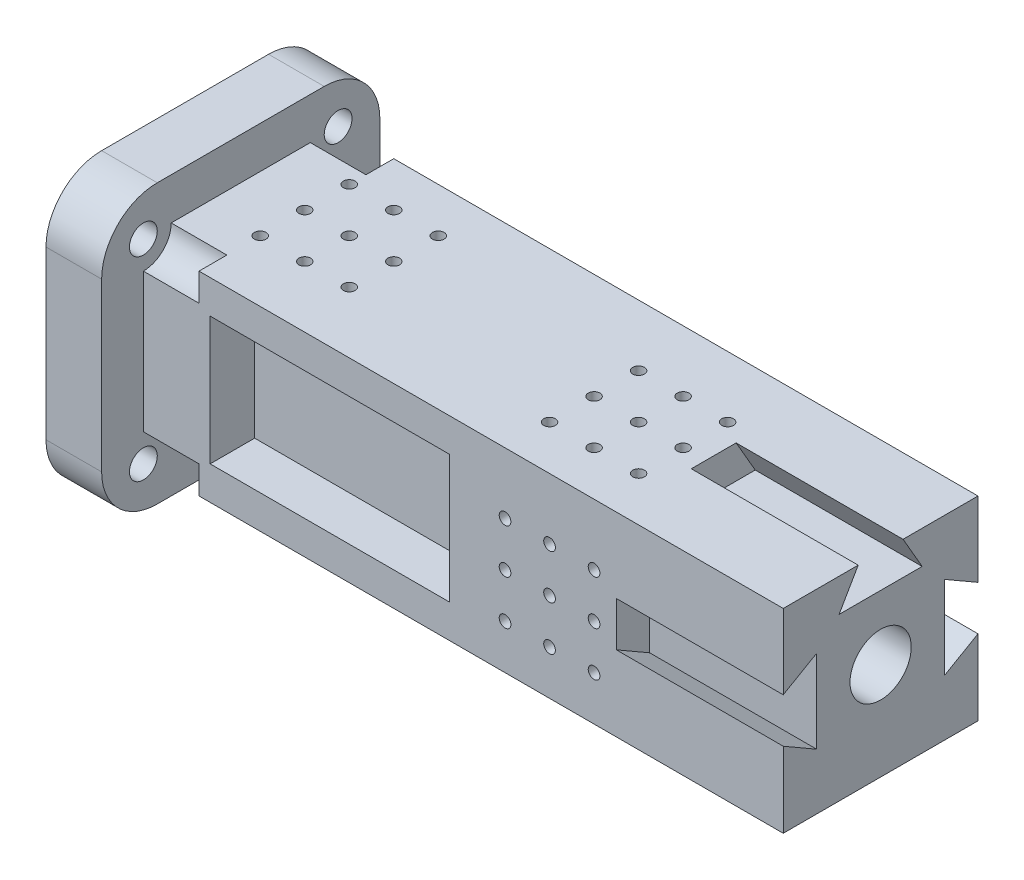
SolidWorks part; units mm, degrees
ref_plane "Front Plane" through (0, 0, 0) normal (0, 0, 1) x (1, 0, 0)
ref_plane "Top Plane" through (0, 0, 0) normal (0, 1, 0) x (1, 0, 0)
ref_plane "Right Plane" through (0, 0, 0) normal (1, 0, 0) x (0, 0, -1)
sketch "Sketch1" plane through (0, 0, 0) normal (1, 0, 0) x (0, 0, -1)
  line L1 (0, 0) -> (35, 0)
  line L2 (0, 0) -> (0, 35)
  line L3 (0, 35) -> (35, 35)
  line L4 (35, 0) -> (35, 35)
  circle A0 centre (17.5, 17.5) radius 5.5
  point P7 (35, 17.5)
  point P9 (17.5, 0)
  dimension "D3" = 11
  dimension "D1" = 35
  dimension "D2" = 35
extrude "Boss-Extrude1" add sketch "Sketch1" along normal blind 115
sketch "Sketch2" plane through (115, 0, 0) normal (1, 0, 0) x (0, 0, -1)
  line L0 (0, 13.5534) -> (6, 10.0893)
  line L1 (0, 35) -> (0, 0) construction
  line L2 (6, 10.0893) -> (6, 25.0175)
  line L3 (6, 25.0175) -> (0, 21.5534)
  line L5 (0.0267, 17.5534) -> (15.3791, 17.5534) construction
  line L6 (17.5, 0.0534) -> (17.5, 32.5624) construction
  line L7 (0, 0) -> (35, 0) construction
  line L20 (0, 21.5534) -> (-1, 21.5534)
  line L21 (-1, 21.5534) -> (-1, 13.5534)
  line L22 (-1, 13.5534) -> (0, 13.5534)
  line L23 (21.5, 35.0534) -> (21.5, 36.0534)
  line L24 (21.5, 36.0534) -> (13.5, 36.0534)
  line L25 (13.5, 36.0534) -> (13.5, 35.0534)
  line L26 (13.5, 35.0534) -> (10.0359, 29.0534)
  line L27 (10.0359, 29.0534) -> (24.9641, 29.0534)
  line L28 (24.9641, 29.0534) -> (21.5, 35.0534)
  line L29 (35, 13.5534) -> (36, 13.5534)
  line L30 (36, 13.5534) -> (36, 21.5534)
  line L31 (36, 21.5534) -> (35, 21.5534)
  line L32 (35, 21.5534) -> (29, 25.0175)
  line L33 (29, 25.0175) -> (29, 10.0893)
  line L34 (29, 10.0893) -> (35, 13.5534)
  line L41 (24.9641, 6.0534) -> (10.0359, 6.0534) [skipped]
  line L42 (10.0359, 6.0534) -> (13.5, 0.0534) [skipped]
  line L43 (13.5, -0.9466) -> (21.5, -0.9466) [skipped]
  line L44 (13.5, 0.0534) -> (13.5, -0.9466) [skipped]
  line L45 (21.5, -0.9466) -> (21.5, 0.0534) [skipped]
  line L46 (21.5, 0.0534) -> (24.9641, 6.0534) [skipped]
  point P27 (17.5, 17.5534)
  point P36 (17.5, 17.5534)
  dimension "D1" = 60
  dimension "D2" = 60
  dimension "D3" = 8
  dimension "D4" = 1
  dimension "D5" = 4
  dimension "D6" = 17.5534
  dimension "D7" = 17.5
  dimension "D9" = 4
  dimension "D10" = 4
  dimension "D11" = 6
  dimension "D8" = 4
extrude "Cut-Extrude2" cut sketch "Sketch2" against normal blind 30
sketch "Sketch3" plane through (0, 0, 0) normal (-1, 0, 0) x (0, 0, 1)
  line L1 (-42.5, -7.5) -> (7.5, -7.5)
  line L2 (-42.5, -7.5) -> (-42.5, 42.5)
  line L3 (-42.5, 42.5) -> (7.5, 42.5)
  line L4 (7.5, -7.5) -> (7.5, 42.5)
  line L5 (-42.5, -7.5) -> (7.5, 42.5) construction
  line L6 (-42.5, 42.5) -> (7.5, -7.5) construction
  circle A0 centre (-17.5, 17.5) radius 5.5
  point P0 (-17.5, 17.5)
  dimension "D3" = 11
  dimension "D1" = 50
  dimension "D2" = 50
extrude "Boss-Extrude2" add sketch "Sketch3" along normal blind 10
sketch "Sketch4" plane through (-10, 0, 0) normal (-1, 0, 0) x (0, 0, 1)
  circle A1 centre (-35, 35) radius 2.5
  circle A2 centre (-35, 0) radius 2.5
  circle A3 centre (0, 0) radius 2.5
  circle A4 centre (0, 35) radius 2.5
  point P14 (-17.5, 17.5)
  dimension "D1" = 17.5
  dimension "D2" = 5
  dimension "D4" = 17.5
  dimension "D3" = 4
extrude "Cut-Extrude3" cut sketch "Sketch4" against normal blind 15
sketch "Sketch6" plane through (0, 0, 0) normal (0, 0, 1) x (-1, 0, 0)
  line L0 (0, -16) -> (-257.9227, -16) construction
  line L1 (-115, -13.5534) -> (-115, 0) construction
  line L3 (-115, -35) -> (-5, -35) construction
  circle A0 centre (-65, -8) radius 1.05
  circle A1 centre (-73, -8) radius 1.05
  circle A2 centre (-81, -8) radius 1.05
  circle A3 centre (-73, -16) radius 1.05
  circle A4 centre (-81, -16) radius 1.05
  circle A5 centre (-73, -24) radius 1.05
  circle A6 centre (-81, -24) radius 1.05
  circle A7 centre (-65, -16) radius 1.05
  circle A8 centre (-65, -24) radius 1.05
  dimension "D3" = 2.1
  dimension "D4" = 8
  dimension "D5" = 8
  dimension "D6" = 34
  dimension "D7" = 19
  dimension "D1" = 3
  dimension "D2" = 3
sketch "Sketch7" plane through (0, 35, 0) normal (0, 1, 0) x (-1, 0, 0)
  line L0 (0, -16) -> (-231.7822, -16) construction
  line L3 (-115, -35) -> (-5, -35) construction
  line L4 (-115, -13.4692) -> (-115, 0) construction
  circle A0 centre (-65, -8) radius 1.05
  circle A1 centre (-73, -8) radius 1.05
  circle A2 centre (-81, -8) radius 1.05
  circle A3 centre (-73, -16) radius 1.05
  circle A4 centre (-81, -16) radius 1.05
  circle A5 centre (-73, -24) radius 1.05
  circle A6 centre (-81, -24) radius 1.05
  circle A7 centre (-65, -16) radius 1.05
  circle A8 centre (-65, -24) radius 1.05
  dimension "D3" = 2.1
  dimension "D4" = 8
  dimension "D5" = 8
  dimension "D6" = 34
  dimension "D7" = 19
  dimension "D1" = 3
  dimension "D2" = 3
sketch "Sketch8" plane through (0, 0, -35) normal (0, 0, -1) x (1, 0, 0)
  line L0 (0, -19) -> (262.5218, -19) construction
  line L2 (115, 0) -> (5, 0) construction
  line L3 (115, 0) -> (115, -13.5534) construction
  circle A0 centre (81, -11) radius 1.05
  circle A1 centre (73, -11) radius 1.05
  circle A2 centre (65, -11) radius 1.05
  circle A3 centre (73, -19) radius 1.05
  circle A4 centre (65, -19) radius 1.05
  circle A5 centre (73, -27) radius 1.05
  circle A6 centre (65, -27) radius 1.05
  circle A7 centre (81, -19) radius 1.05
  circle A8 centre (81, -27) radius 1.05
  dimension "D3" = 2.1
  dimension "D4" = 8
  dimension "D5" = 8
  dimension "D6" = 34
  dimension "D7" = 19
  dimension "D1" = 3
  dimension "D2" = 3
sketch "Sketch9" plane through (0, 0, 0) normal (0, -1, 0) x (1, 0, 0)
  line L0 (0, -19) -> (216.7478, -19) construction
  line L1 (115, 0) -> (115, -35) construction
  line L2 (115, 0) -> (5, 0) construction
  line L3 (0, -42.5) -> (0, 7.5) construction
  circle A0 centre (56, -11) radius 1.05
  circle A1 centre (48, -11) radius 1.05
  circle A2 centre (40, -11) radius 1.05
  circle A3 centre (48, -19) radius 1.05
  circle A4 centre (40, -19) radius 1.05
  circle A5 centre (48, -27) radius 1.05
  circle A6 centre (40, -27) radius 1.05
  circle A7 centre (56, -19) radius 1.05
  circle A8 centre (56, -27) radius 1.05
  dimension "D3" = 2.1
  dimension "D4" = 8
  dimension "D5" = 8
  dimension "D6" = 59
  dimension "D7" = 19
  dimension "D1" = 3
  dimension "D2" = 3
extrude "Cut-Extrude4" cut sketch "Sketch6" against normal blind 5
extrude "Cut-Extrude5" cut sketch "Sketch7" against normal blind 5
extrude "Cut-Extrude6" cut sketch "Sketch8" against normal blind 5
extrude "Cut-Extrude7" cut sketch "Sketch9" against normal blind 5
sketch "Sketch11" plane through (0, 35, 0) normal (0, 1, 0) x (-1, 0, 0)
  line L0 (-115, -19) -> (0, -19) construction
  line L1 (-115, -13.4692) -> (-115, 0) construction
  line L2 (-115, -35) -> (-115, -21.5308) construction
  line L4 (0, -32.5) -> (0, -2.5) construction
  line L5 (-115, 0) -> (-5, 0) construction
  circle A0 centre (-10, -11) radius 1.05
  circle A1 centre (-18, -11) radius 1.05
  circle A2 centre (-26, -11) radius 1.05
  circle A3 centre (-18, -19) radius 1.05
  circle A4 centre (-26, -19) radius 1.05
  circle A5 centre (-18, -27) radius 1.05
  circle A6 centre (-26, -27) radius 1.05
  circle A7 centre (-10, -19) radius 1.05
  circle A8 centre (-10, -27) radius 1.05
  dimension "D3" = 2.1
  dimension "D4" = 8
  dimension "D5" = 8
  dimension "D6" = 89
  dimension "D7" = 19
  dimension "D1" = 3
  dimension "D2" = 3
extrude "Cut-Extrude8" cut sketch "Sketch11" against normal blind 5
sketch "Sketch12" plane through (0, 0, 0) normal (0, 0, 1) x (1, 0, 0)
  line L0 (115, 35) -> (5, 35) construction
  line L1 (12, 29) -> (55, 29)
  line L11 (12, 6) -> (55, 6)
  line L13 (115, 0) -> (5, 0) construction
  line L20 (12, 29) -> (12, 6)
  line L21 (55, 29) -> (55, 6)
  line L22 (0, -7.5) -> (0, 42.5) construction
  line L23 (115, 35) -> (115, 21.5534) construction
  dimension "D1" = 12
  dimension "D2" = 60
  dimension "D7" = 6
  dimension "D8" = 6
extrude "Cut-Extrude9" cut sketch "Sketch12" against normal blind 8
sketch "Sketch13" plane through (0, 0, -35) normal (0, 0, -1) x (-1, 0, 0)
  line L1 (-55, 29) -> (-15, 29)
  line L11 (-55, 6) -> (-15, 6)
  line L17 (-115, 35) -> (-5, 35) construction
  line L20 (-55, 29) -> (-55, 6)
  line L21 (-15, 29) -> (-15, 6)
  line L22 (-115, 0) -> (-5, 0) construction
  line L23 (0, 2.5) -> (0, 32.5) construction
  line L24 (-115, 21.5534) -> (-115, 35) construction
  dimension "D1" = 60
  dimension "D2" = 6
  dimension "D3" = 15
  dimension "D8" = 6
extrude "Cut-Extrude10" cut sketch "Sketch13" against normal blind 8
fillet "Fillet1" radius 10 4 edges at (-5, -7.5, -42.5) (-5, -7.5, 7.5) (-5, 42.5, 7.5) (-5, 42.5, -42.5)
sketch "Sketch14" plane through (0, 0, 0) normal (1, 0, 0) x (0, 0, -1)
  circle A0 centre (0, 0) radius 5
  circle A1 centre (35, 0) radius 5
  circle A2 centre (35, 35) radius 5
  circle A3 centre (0, 35) radius 5
  dimension "D1" = 10
  dimension "D2" = 2
  dimension "D3" = 2
extrude "Cut-Extrude11" cut sketch "Sketch14" along normal blind 10
sketch "Sketch15" plane through (0, 0, 0) normal (0, -1, 0) x (1, 0, 0)
  line L0 (115, -17.5) -> (80.7458, -17.5) construction
  line L1 (115, 0) -> (115, -35) construction
  line L2 (100, -35) -> (100, 0) construction
  line L3 (115, -35) -> (10, -35) construction
  line L4 (115, 0) -> (10, 0) construction
  circle A0 centre (100, -17.5) radius 2.5
  point P12 (0, 0)
  dimension "D1" = 5
  dimension "D2" = 15
extrude "Cut-Extrude12" cut sketch "Sketch15" against normal up to next
